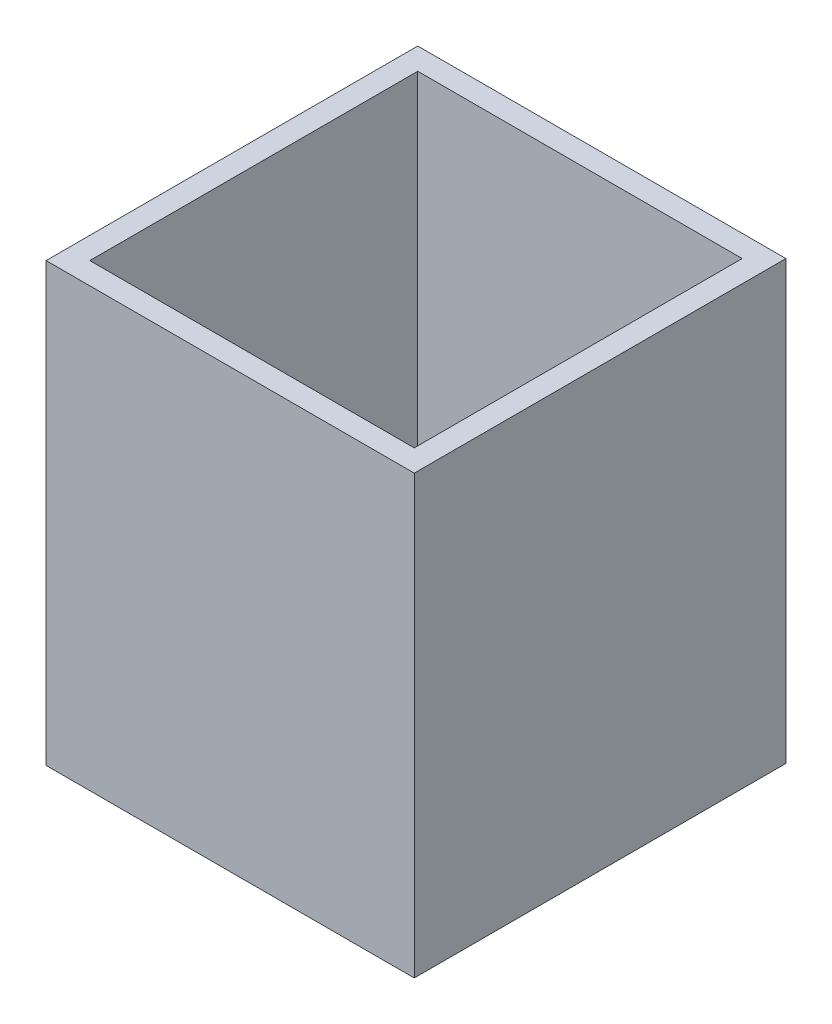
SolidWorks part; units mm, degrees
material "Balsa"
ref_plane "Front Plane" through (0, 0, 0) normal (0, 0, 1) x (1, 0, 0)
ref_plane "Top Plane" through (0, 0, 0) normal (0, 1, 0) x (1, 0, 0)
ref_plane "Right Plane" through (0, 0, 0) normal (1, 0, 0) x (0, 0, -1)
sketch "Sketch2" plane through (0, 0, 0) normal (0, 1, 0) x (1, 0, 0)
  line L1 (-53.467, -53.975) -> (53.467, -53.975)
  line L2 (-53.467, -53.975) -> (-53.467, 53.975)
  line L3 (-53.467, 53.975) -> (53.467, 53.975)
  line L4 (53.467, -53.975) -> (53.467, 53.975)
  line L5 (-53.467, -53.975) -> (53.467, 53.975) construction
  line L6 (-53.467, 53.975) -> (53.467, -53.975) construction
  point P0 (0, 0)
  dimension "D1" = 106.934
  dimension "D2" = 107.95
extrude "Boss-Extrude1" add sketch "Sketch2" along normal blind 127
shell "Shell1" thickness 6.35
